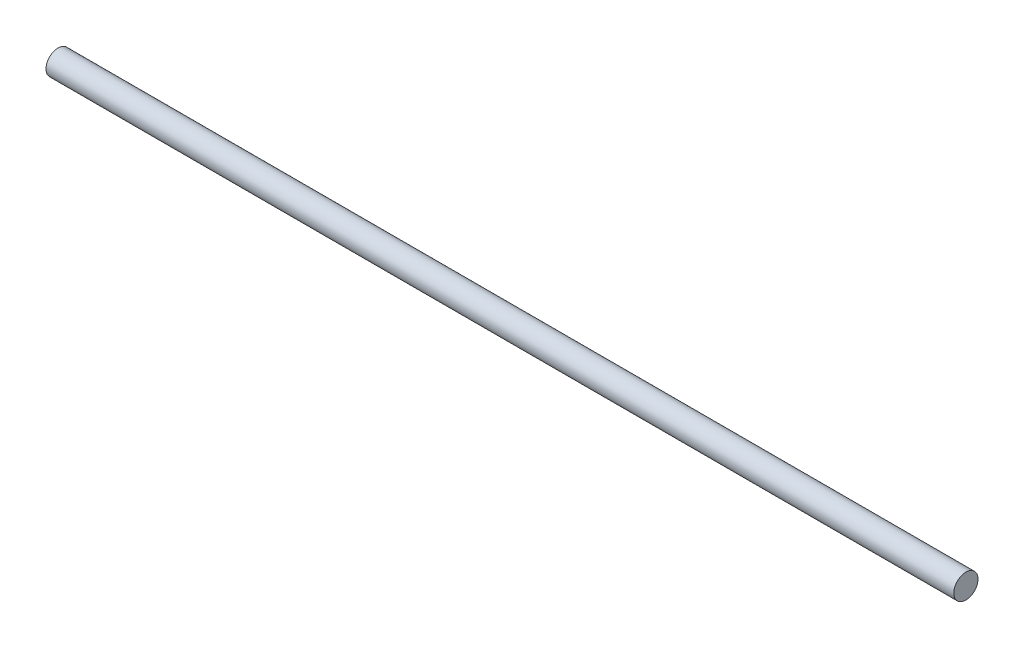
SolidWorks part; units mm, degrees
material "Plain Carbon Steel"
ref_plane "Front Plane" through (0, 0, 0) normal (0, 0, 1) x (1, 0, 0)
ref_plane "Top Plane" through (0, 0, 0) normal (0, 1, 0) x (1, 0, 0)
ref_plane "Right Plane" through (0, 0, 0) normal (1, 0, 0) x (0, 0, -1)
sketch "Sketch1" plane through (0, 0, 0) normal (1, 0, 0) x (0, 0, -1)
  circle A0 centre (0, 0) radius 4
  dimension "D1" = 8
extrude "Boss-Extrude1" add sketch "Sketch1" against normal blind 300
